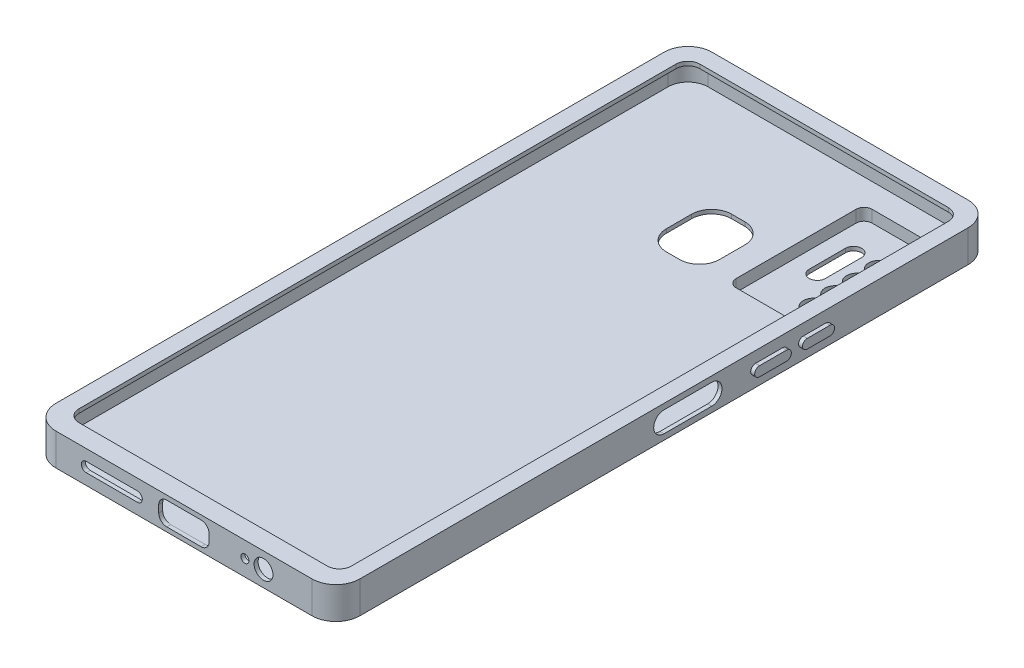
SolidWorks part; units mm, degrees
material "PVC 0.007 Plasticized"
ref_plane "Front Plane" through (0, 0, 0) normal (0, 0, 1) x (1, 0, 0)
ref_plane "Top Plane" through (0, 0, 0) normal (0, 1, 0) x (1, 0, 0)
ref_plane "Right Plane" through (0, 0, 0) normal (1, 0, 0) x (0, 0, -1)
sketch "Sketch1" plane through (0, 0, 0) normal (0, 1, 0) x (1, 0, 0)
  line L1 (0, 0) -> (76, 0)
  line L2 (0, 0) -> (0, 164)
  line L3 (0, 164) -> (76, 164)
  line L4 (76, 0) -> (76, 164)
  dimension "D1" = 164
  dimension "D2" = 76
extrude "Boss-Extrude1" add sketch "Sketch1" along normal blind 8
fillet "Fillet1" radius 6 4 edges at (76, 4, -164) (0, 4, -164) (0, 4, 0) (76, 4, 0)
shell "Shell1" thickness 1
sketch "Sketch2" plane through (0, 8, 0) normal (0, 1, 0) x (1, 0, 0)
  line L1 (4.0646, 159.9024) -> (72.1555, 159.9024)
  line L2 (4.0646, 159.9024) -> (4.0646, 4.6933)
  line L3 (4.0646, 4.6933) -> (72.1555, 4.6933)
  line L4 (72.1555, 159.9024) -> (72.1555, 4.6933)
extrude "Cut-Extrude1" cut sketch "Sketch2" against normal up to next
fillet "Fillet2" radius 3 4 edges at (72.1555, 7.5, -4.6933) (4.0646, 7.5, -4.6933) (72.1555, 7.5, -159.9024) (4.0646, 7.5, -159.9024)
sketch "Sketch4" plane through (0, 0, 0) normal (0, -1, 0) x (1, 0, 0)
  line L0 (71.3364, -158.021) -> (71.3364, -121.2899)
  line L1 (71.3364, -121.2899) -> (49.792, -121.2899)
  line L2 (49.792, -121.2899) -> (49.792, -158.021)
  line L3 (49.792, -158.021) -> (71.3364, -158.021)
extrude "Boss-Extrude2" add sketch "Sketch4" along normal blind 4
sketch "Sketch6" plane through (0, -4, 0) normal (0, -1, 0) x (1, 0, 0)
  line L0 (52.4133, -124.0811) -> (68.8274, -124.0811)
  line L1 (68.8274, -124.0811) -> (68.8274, -155.3875)
  line L2 (68.8274, -155.3875) -> (52.4133, -155.3875)
  line L3 (52.4133, -155.3875) -> (52.4133, -124.0811)
extrude "Cut-Extrude2" cut sketch "Sketch6" against normal blind 1
fillet "Fillet3" radius 2 8 edges at (68.8274, -3.5, -155.3875) (52.4133, -3.5, -155.3875) (68.8274, -3.5, -124.0811) (71.3364, -2, -121.2899) (49.792, -2, -158.021) (71.3364, -2, -158.021) (52.4133, -3.5, -124.0811) (49.792, -2, -121.2899)
sketch "Sketch8" plane through (0, -3, 0) normal (0, -1, 0) x (1, 0, 0)
  line L0 (63.7756, -124.5654) -> (63.7756, -160.9398) construction
  circle A0 centre (63.7756, -131.6982) radius 3
  circle A1 centre (63.7756, -137.0832) radius 3
  circle A2 centre (63.7756, -142.4681) radius 3
  circle A3 centre (63.7756, -147.9278) radius 3
  point P4 (64.1495, -131.6982)
  point P7 (64.1495, -138.3546)
  point P10 (64.1495, -145.1606)
  point P13 (64.1495, -150.9943)
  point P14 (63.9999, -137.0832)
  point P15 (63.9999, -142.4681)
  point P16 (63.7756, -147.9278)
extrude "Boss-Extrude4" add sketch "Sketch8" along normal blind 1 contours A2 L0 A3 | L0 A3 A2 | L0 A2 A3 | A3 L0 A2 | A1 L0 A3 A2 | L0 A1 A2 A3 | A0 L0 A2 A1 | L0 A0 A1 A2 | A0 L0 A1 | L0 A0 A1 | L0 A1 A0 | A1 L0 A0 | A2 L0 A1 | L0 A2 A1
sketch "Sketch9" plane through (0, -4, 0) normal (0, -1, 0) x (1, 0, 0)
  line L0 (63.7634, -126.7026) -> (63.7634, -159.5168) construction
  circle A0 centre (63.7634, -131.637) radius 2.5887
  circle A1 centre (63.7634, -137.0423) radius 2.5887
  circle A2 centre (63.7634, -142.4598) radius 2.5887
  circle A3 centre (63.7634, -147.954) radius 2.5887
  point P4 (63.709, -131.4367)
  point P5 (0, 0)
  point P6 (63.7288, -131.6716)
  point P7 (63.7634, -131.637)
  point P10 (63.7634, -137.0423)
  point P13 (63.7634, -142.4598)
  point P16 (63.7634, -147.954)
extrude "Cut-Extrude3" cut sketch "Sketch9" against normal through all
sketch "Sketch10" plane through (0, -3, 0) normal (0, -1, 0) x (1, 0, 0)
  line L0 (57.1285, -148.2429) -> (57.1285, -139.1733) construction
  line L1 (55.113, -148.2429) -> (55.113, -139.1733)
  line L2 (59.1439, -148.2429) -> (59.1439, -139.1733)
  arc A0 (55.113, -148.2429) -> (59.1439, -148.2429) centre (57.1285, -148.2429) ccw
  arc A1 (59.1439, -139.1733) -> (55.113, -139.1733) centre (57.1285, -139.1733) ccw
  point P2 (57.1285, -143.7081)
extrude "Cut-Extrude4" cut sketch "Sketch10" against normal through all
sketch "Sketch11" plane through (0, 0, 0) normal (0, -1, 0) x (1, 0, 0)
  line L0 (38.1575, -51.4399) -> (38.1575, -193.0482) construction
  line L2 (31.5045, -122.0669) -> (44.8105, -122.0669)
  line L3 (31.5045, -122.0669) -> (31.5045, -138.3865)
  line L4 (31.5045, -138.3865) -> (44.8105, -138.3865)
  line L5 (44.8105, -122.0669) -> (44.8105, -138.3865)
  line L6 (31.5045, -122.0669) -> (44.8105, -138.3865) construction
  line L7 (31.5045, -138.3865) -> (44.8105, -122.0669) construction
  point P2 (38.1575, -130.2267)
extrude "Cut-Extrude5" cut sketch "Sketch11" against normal through all
fillet "Fillet4" radius 5 4 edges at (44.8105, 0.5, -138.3865) (31.5045, 0.5, -122.0669) (31.5045, 0.5, -138.3865) (44.8105, 0.5, -122.0669)
sketch "Sketch12" plane through (0, 1, 0) normal (0, 1, 0) x (1, 0, 0)
  line L0 (70, 164) -> (6, 164) construction
  line L1 (51, 157) -> (70, 157)
  line L2 (51, 157) -> (51, 123)
  line L3 (51, 123) -> (70, 123)
  line L4 (70, 157) -> (70, 123)
  line L5 (76, 6) -> (76, 158) construction
  dimension "D1" = 19
  dimension "D2" = 34
  dimension "D3" = 7
  dimension "D4" = 6
extrude "Cut-Extrude6" cut sketch "Sketch12" against normal blind 3
fillet "Fillet5" radius 2 4 edges at (51, -0.5, -157) (70, -0.5, -157) (70, -0.5, -123) (51, -0.5, -123)
sketch "Sketch13" plane through (0, 0, 0) normal (0, 0, 1) x (1, 0, 0)
  line L2 (38, 19.2343) -> (38, -16.3411) construction
  line L3 (70, 0) -> (70, 8) construction
  line L5 (-2.3124, 4) -> (77.9235, 4) construction
  line L6 (6, 8) -> (70, 8) construction
  line L7 (13.5876, 4) -> (26.3763, 4) construction
  line L8 (31.7028, 6.8897) -> (44.2972, 6.8897)
  line L9 (31.7028, 6.8897) -> (31.7028, 1.1103)
  line L10 (31.7028, 1.1103) -> (44.2972, 1.1103)
  line L11 (44.2972, 6.8897) -> (44.2972, 1.1103)
  line L12 (31.7028, 6.8897) -> (44.2972, 1.1103) construction
  line L13 (31.7028, 1.1103) -> (44.2972, 6.8897) construction
  line L14 (13.5876, 5.2266) -> (26.3763, 5.2266)
  line L15 (13.5876, 2.7734) -> (26.3763, 2.7734)
  arc A0 (13.5876, 5.2266) -> (13.5876, 2.7734) centre (13.5876, 4) ccw
  arc A1 (26.3763, 2.7734) -> (26.3763, 5.2266) centre (26.3763, 4) ccw
  circle A2 centre (53.2479, 4) radius 1
  circle A3 centre (57.898, 4) radius 2.3589
  point P8 (38, 4)
  point P13 (19.9819, 4)
  point P24 (57.898, 4)
  dimension "D1" = 32
  dimension "D2" = 4
extrude "Cut-Extrude7" cut sketch "Sketch13" against normal blind 3
fillet "Fillet6" radius 2 4 edges at (31.7028, 6.8897, -0.5) (31.7028, 1.1103, -0.5) (44.2972, 6.8897, -0.5) (44.2972, 1.1103, -0.5)
sketch "Sketch14" plane through (76, 0, 0) normal (1, 0, 0) x (0, 0, -1)
  line L2 (82, 4) -> (93.9086, 4) construction
  line L3 (82, 6.5831) -> (93.9086, 6.5831)
  line L4 (82, 1.4169) -> (93.9086, 1.4169)
  line L5 (6, 8) -> (158, 8) construction
  line L7 (6, 8) -> (6, 0) construction
  arc A0 (82, 6.5831) -> (82, 1.4169) centre (82, 4) ccw
  arc A1 (93.9086, 1.4169) -> (93.9086, 6.5831) centre (93.9086, 4) ccw
  point P0 (87.9543, 4)
  point P11 (0, 0)
  point P12 (93.9086, 4)
  dimension "D2" = 76
  dimension "D1" = 4
extrude "Cut-Extrude8" cut sketch "Sketch14" against normal blind 3
sketch "Sketch16" plane through (76, 0, 0) normal (1, 0, 0) x (0, 0, -1)
  line L0 (98.1221, 4) -> (133.7898, 4) construction
  line L1 (6, 8) -> (158, 8) construction
  line L2 (104.869, 4) -> (111.6092, 4) construction
  line L3 (104.869, 5.2084) -> (111.6092, 5.2084)
  line L4 (104.869, 2.7916) -> (111.6092, 2.7916)
  line L5 (116.7728, 4) -> (122.4702, 4) construction
  line L6 (116.7728, 5.1602) -> (122.4702, 5.1602)
  line L7 (116.7728, 2.8398) -> (122.4702, 2.8398)
  arc A0 (104.869, 5.2084) -> (104.869, 2.7916) centre (104.869, 4) ccw
  arc A1 (111.6092, 2.7916) -> (111.6092, 5.2084) centre (111.6092, 4) ccw
  arc A2 (116.7728, 5.1602) -> (116.7728, 2.8398) centre (116.7728, 4) ccw
  arc A3 (122.4702, 2.8398) -> (122.4702, 5.1602) centre (122.4702, 4) ccw
  point P6 (108.2391, 4)
  point P11 (119.6215, 4)
  dimension "D1" = 4
extrude "Boss-Extrude5" add sketch "Sketch16" along normal blind 1 and the other way blind 1.05
sketch "Sketch18" plane through (75, 0, 0) normal (-1, 0, 0) x (0, 0, 1)
  line L0 (-125.1661, 4.0706) -> (-101.524, 4.0706) construction
  line L1 (-125.1661, 6.3477) -> (-101.524, 6.3477)
  line L2 (-125.1661, 1.7934) -> (-101.524, 1.7934)
  arc A0 (-125.1661, 6.3477) -> (-125.1661, 1.7934) centre (-125.1661, 4.0706) ccw
  arc A1 (-101.524, 1.7934) -> (-101.524, 6.3477) centre (-101.524, 4.0706) ccw
  point P2 (-113.345, 4.0706)
extrude "Cut-Extrude10" cut sketch "Sketch18" against normal blind 0.5
